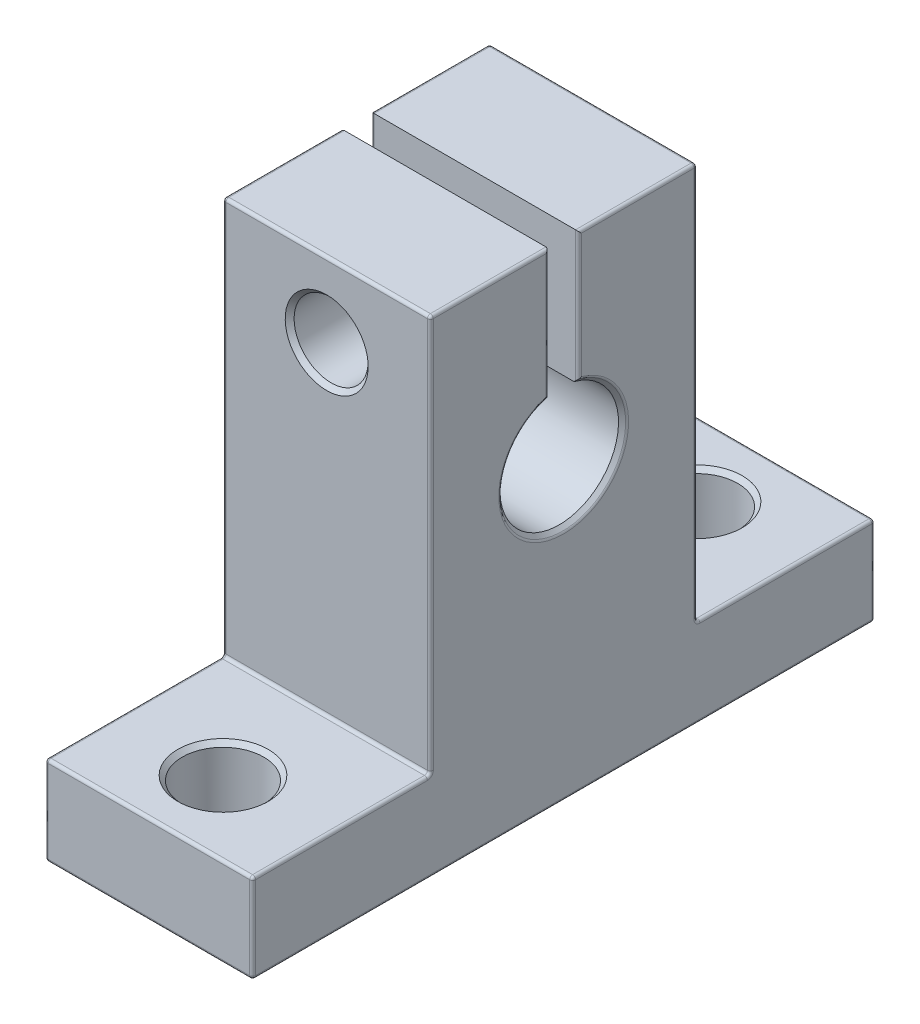
SolidWorks part; units mm, degrees
material "АМг 2 ГОСТ 4784-97"
ref_plane "Front Plane" through (0, 0, 0) normal (0, 0, 1) x (1, 0, 0)
ref_plane "Top Plane" through (0, 0, 0) normal (0, 1, 0) x (1, 0, 0)
ref_plane "Right Plane" through (0, 0, 0) normal (1, 0, 0) x (0, 0, -1)
sketch "Sketch1" plane through (0, 0, 0) normal (1, 0, 0) x (0, 0, -1)
  line L0 (-21, 0) -> (21, 0)
  line L1 (-21, 0) -> (-21, 6)
  line L2 (-21, 6) -> (-9, 6)
  line L3 (-9, 6) -> (-9, 32.8)
  line L4 (-9, 32.8) -> (-1, 32.8)
  line L5 (9, 32.8) -> (9, 6)
  line L6 (9, 6) -> (21, 6)
  line L7 (21, 6) -> (21, 0)
  line L8 (0, 0) -> (0, 37.5052) construction
  line L9 (1, 32.8) -> (9, 32.8)
  line L10 (1, 23.873) -> (1, 32.8)
  line L11 (-1, 23.873) -> (-1, 32.8)
  arc A0 (-1, 23.873) -> (1, 23.873) centre (0, 20) ccw
  dimension "D8" = 20
  dimension "D3" = 8
  dimension "D1" = 32.8
  dimension "D2" = 18
  dimension "D4" = 6
  dimension "D5" = 6
  dimension "D6" = 42
  dimension "D7" = 2
extrude "Boss-Extrude1" add sketch "Sketch1" along normal mid plane 14
sketch "Sketch4" plane through (0, 6, 0) normal (0, 1, 0) x (1, 0, 0)
  line L0 (7, -21) -> (-7, -21) construction
  line L1 (7, 21) -> (-7, 21) construction
  line L2 (7, -9) -> (7, -21) construction
  circle A0 centre (0, -16) radius 2.75
  circle A1 centre (0, 16) radius 2.75
  dimension "D3" = 5.5
  dimension "D4" = 32
  dimension "D1" = 5
  dimension "D2" = 5
  dimension "D5" = 7
extrude "Cut-Extrude3" cut sketch "Sketch4" against normal through all
sketch "Sketch6" plane through (0, 0, -9) normal (0, 0, -1) x (-1, 0, 0)
  line L0 (-7, 32.8) -> (7, 32.8) construction
  circle A0 centre (0, 27.8) radius 2.5
  dimension "D2" = 5
  dimension "D1" = 5
extrude "Cut-Extrude4" cut sketch "Sketch6" against normal through all
sketch "Sketch7" plane through (0, 0, -9) normal (0, 0, -1) x (-1, 0, 0)
  circle A0 centre (0, 27.8) radius 4
  dimension "D1" = 8
extrude "Cut-Extrude5" cut sketch "Sketch7" against normal blind 5
chamfer "Фаска1" distance 0.3 angle 45 8 edges at (0, 30.3, 9) (0, 31.8, -9) (0, 6, 18.75) (0, 6, -13.25) (-7, 16, 0) (7, 16, 0) (0, 0, -13.25) (0, 0, 18.75)
fillet "Скругление1" radius 0.2 32 edges at (-7, 32.8, 5) (-7, 19.4, 9) (-7, 6, 15) (-7, 3, 21) (-7, 0, 0) (-7, 3, -21) (-7, 6, -15) (-7, 19.4, -9) (-7, 32.8, -5) (-7, 28.4911, -1) (-7, 15.7, 0) (-7, 28.4911, 1) (7, 32.8, -5) (7, 19.4, -9) (7, 6, -15) (7, 3, -21) (7, 0, 0) (7, 3, 21) (7, 6, 15) (7, 19.4, 9) (7, 32.8, 5) (7, 28.4911, 1) (7, 15.7, 0) (7, 28.4911, -1) (0, 0, 21) (0, 6, 9) (0, 6, 21) (0, 32.8, 9) (0, 0, -21) (0, 32.8, -9) (0, 6, -9) (0, 6, -21)
